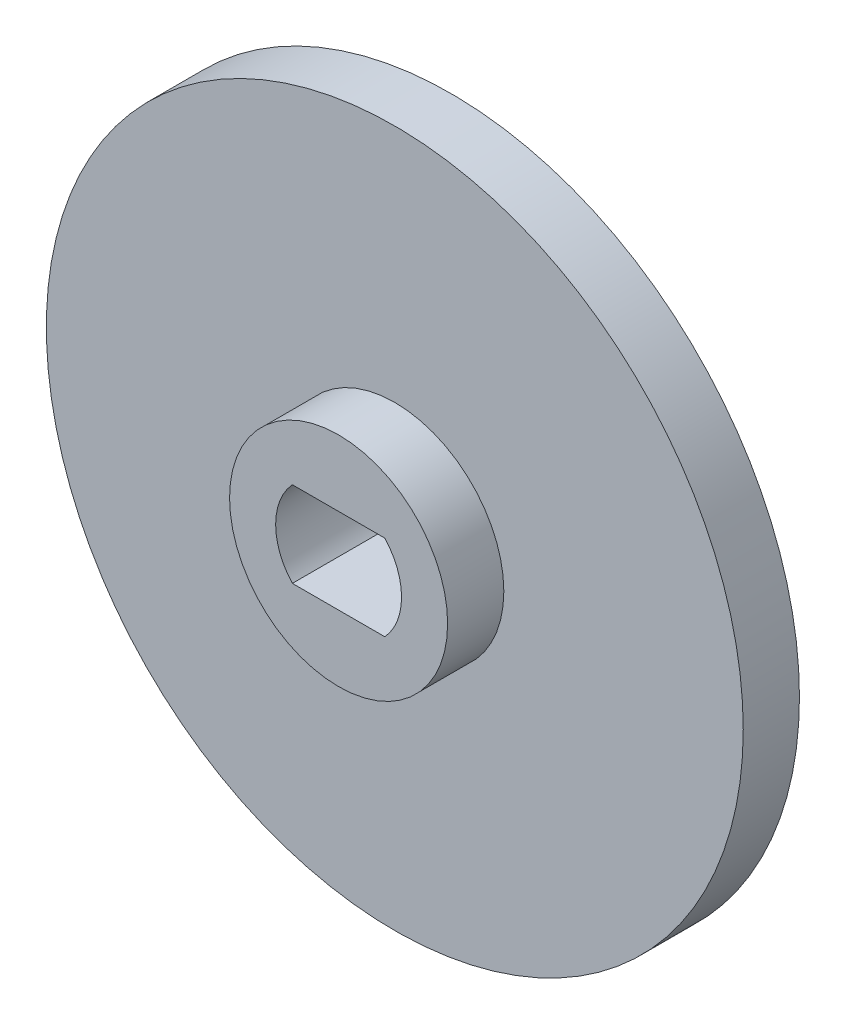
SolidWorks part; units mm, degrees
ref_plane "Front Plane" through (0, 0, 0) normal (0, 0, 1) x (1, 0, 0)
ref_plane "Top Plane" through (0, 0, 0) normal (0, 1, 0) x (1, 0, 0)
ref_plane "Right Plane" through (0, 0, 0) normal (1, 0, 0) x (0, 0, -1)
sketch "Sketch1" plane through (0, 0, 0) normal (0, 0, 1) x (1, 0, 0)
  circle A0 centre (0, 0) radius 15.5 construction
  circle A1 centre (0, 0) radius 15.5
extrude "Boss-Extrude1" add sketch "Sketch1" along normal blind 2.5
sketch "Sketch2" plane through (0, 0, 0) normal (0, 0, -1) x (-1, 0, 0)
  line L0 (-7.8174, 8.129) -> (-3.5527, 4.927)
  line L1 (0.2749, 6.0681) -> (2.0901, 11.0826)
  line L2 (-7.8774, 8.0491) -> (-3.6127, 4.8471)
  line L3 (0.3689, 6.0341) -> (2.1842, 11.0485)
  line L4 (-7.8774, 8.0491) -> (-3.6127, 4.8471) construction
  line L5 (0.3689, 6.0341) -> (2.1842, 11.0485) construction
  arc A0 (1.3416, 12.2836) -> (-7.8486, 9.5439) centre (0, 0) ccw
  arc A1 (-7.8486, 9.5439) -> (-7.8174, 8.129) centre (-7.277, 8.8488) ccw
  arc A2 (-3.5527, 4.927) -> (-2.5887, 4.8527) centre (-3.0123, 5.6468) ccw
  arc A3 (-0.491, 5.478) -> (-2.5887, 4.8527) centre (0, 0) ccw
  arc A4 (-0.491, 5.478) -> (0.2749, 6.0681) centre (-0.5714, 6.3744) ccw
  arc A5 (2.0901, 11.0826) -> (1.3416, 12.2836) centre (1.2439, 11.3889) ccw
  arc A6 (1.3524, 12.383) -> (-7.9122, 9.6211) centre (0, 0) ccw
  arc A7 (-7.9122, 9.6211) -> (-7.8774, 8.0491) centre (-7.277, 8.8488) ccw
  arc A8 (-3.6127, 4.8471) -> (-2.5416, 4.7645) centre (-3.0123, 5.6468) ccw
  arc A9 (-0.4821, 5.3784) -> (-2.5416, 4.7645) centre (0, 0) ccw
  arc A10 (-0.4821, 5.3784) -> (0.3689, 6.0341) centre (-0.5714, 6.3744) ccw
  arc A11 (2.1842, 11.0485) -> (1.3524, 12.383) centre (1.2439, 11.3889) ccw
  arc A12 (1.3524, 12.383) -> (-7.9122, 9.6211) centre (0, 0) ccw construction
  arc A13 (-7.9122, 9.6211) -> (-7.8774, 8.0491) centre (-7.277, 8.8488) ccw construction
  arc A14 (-3.6127, 4.8471) -> (-2.5416, 4.7645) centre (-3.0123, 5.6468) ccw construction
  arc A15 (-0.4821, 5.3784) -> (-2.5416, 4.7645) centre (0, 0) ccw construction
  arc A16 (-0.4821, 5.3784) -> (0.3689, 6.0341) centre (-0.5714, 6.3744) ccw construction
  arc A17 (2.1842, 11.0485) -> (1.3524, 12.383) centre (1.2439, 11.3889) ccw construction
  dimension "D1" = 0
  dimension "D2" = 0.1
extrude "Boss-Extrude2" add sketch "Sketch2" along normal offset from surface (1.9 mm away) 0.3
pattern_circular "CirPattern1" count 5 over 360 about axis through (0, 0, 0) along (0, 0, 1) of "Boss-Extrude2"
sketch "Sketch3" plane through (0, 0, 0) normal (0, 0, 1) x (1, 0, 0)
  circle A0 centre (0, 0) radius 4.85
  dimension "D1" = 9.7
extrude "Boss-Extrude3" add sketch "Sketch3" along normal blind 2.5 from surface at 2.5 starting at face at (15.5, 0, 2.5)
sketch "Sketch4" plane through (0, 0, 0) normal (0, 0, 1) x (1, 0, 0)
  circle A0 centre (0, 0) radius 2
  dimension "D1" = 4
extrude "Cut-Extrude1" [suppressed] cut sketch "Sketch4" along normal through all
sketch "Sketch5" plane through (0, 0, 5) normal (0, 0, 1) x (1, 0, 0)
  line L0 (-2.0567, 1.9) -> (2.0567, 1.9)
  line L1 (2.0567, -1.9) -> (-2.0567, -1.9)
  arc A0 (-2.0567, 1.9) -> (-2.0567, -1.9) centre (0, 0) ccw
  arc A1 (2.0567, -1.9) -> (2.0567, 1.9) centre (0, 0) ccw
  dimension "D1" = 5.6
  dimension "D2" = 3.8
extrude "Cut-Extrude2" cut sketch "Sketch5" against normal through all
sketch "Sketch6" plane through (0, 0, 0) normal (0, 0, -1) x (-1, 0, 0)
  circle A1 centre (0, 0) radius 15.5 construction
  circle A2 centre (0, 0) radius 15.5
  circle A3 centre (0, 0) radius 13.5
  dimension "D1" = 2
extrude "Boss-Extrude4" [suppressed] add sketch "Sketch6" along normal offset from surface (0.9 mm away) 0.1
